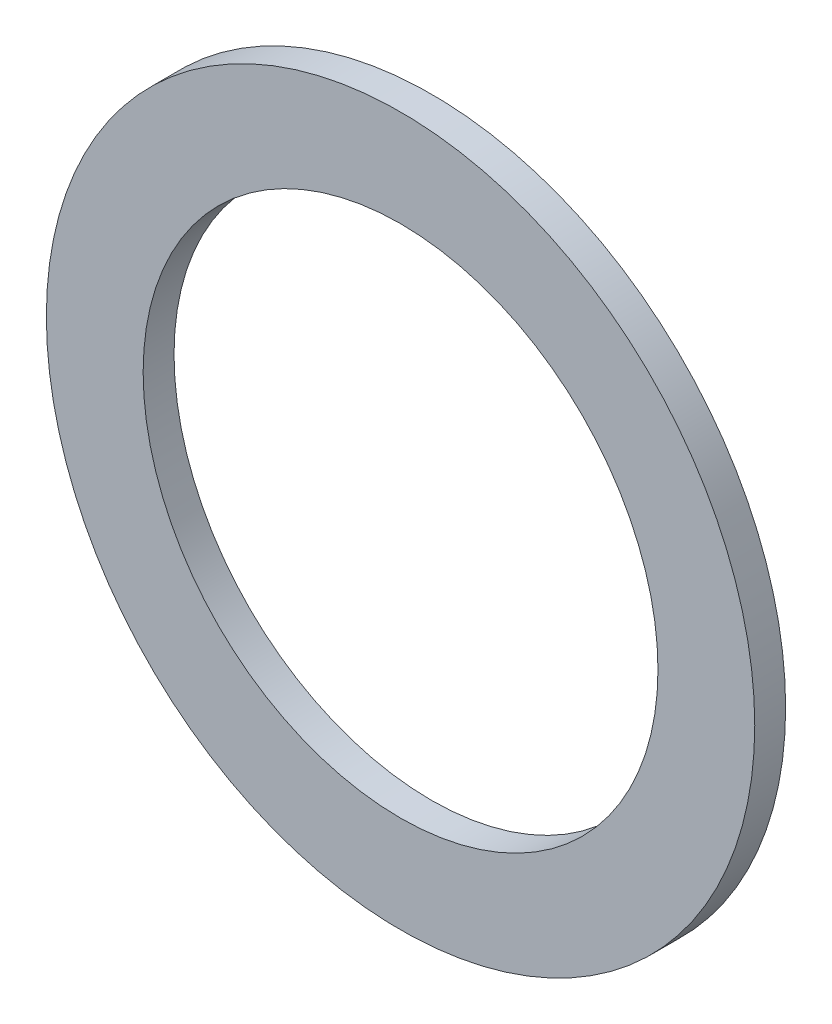
SolidWorks part; units mm, degrees
material "Nylon 101"
ref_plane "Front Plane" through (0, 0, 0) normal (0, 0, 1) x (1, 0, 0)
ref_plane "Top Plane" through (0, 0, 0) normal (0, 1, 0) x (1, 0, 0)
ref_plane "Right Plane" through (0, 0, 0) normal (1, 0, 0) x (0, 0, -1)
sketch "Sketch1" plane through (0, 0, 0) normal (0, 0, 1) x (1, 0, 0)
  circle A0 centre (0, 0) radius 6.35
  circle A1 centre (0, 0) radius 8.7376
  dimension "D1" = 12.7
  dimension "D2" = 17.4752
extrude "Boss-Extrude1" add sketch "Sketch1" along normal blind 0.762
